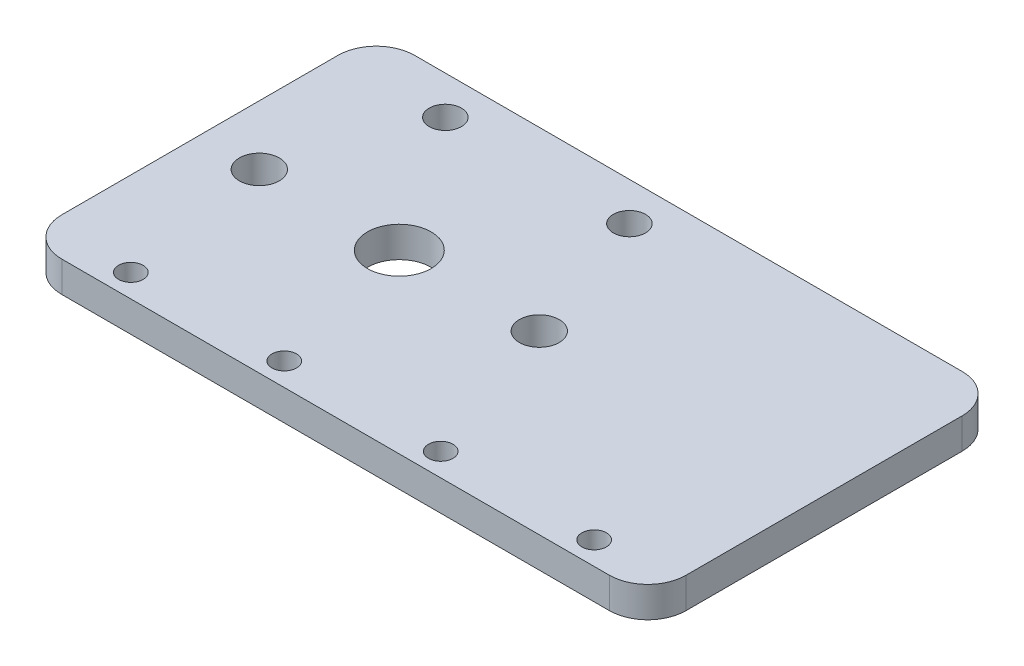
SolidWorks part; units mm, degrees
material "6061 合金"
ref_plane "前视基准面" through (0, 0, 0) normal (0, 0, 1) x (1, 0, 0)
ref_plane "上视基准面" through (0, 0, 0) normal (0, 1, 0) x (1, 0, 0)
ref_plane "右视基准面" through (0, 0, 0) normal (1, 0, 0) x (0, 0, -1)
sketch "草图1" plane through (0, 0, 0) normal (0, 1, 0) x (1, 0, 0)
  line L1 (-26, -23) -> (26, -23)
  line L2 (-26, -23) -> (-26, 23)
  line L3 (-26, 23) -> (26, 23)
  line L4 (26, -23) -> (26, 23)
  line L5 (0, 23) -> (0, -23) construction
  line L6 (-26, 0) -> (26, 0) construction
  circle A0 centre (-18.25, 0) radius 2.6
  circle A1 centre (18.25, 0) radius 2.6
  circle A2 centre (0, 0) radius 4.15
  point P0 (0, 0)
  dimension "D3" = 36.5
  dimension "D4" = 5.2
  dimension "D5" = 8.3
  dimension "D1" = 52
  dimension "D2" = 46
extrude "主板" add sketch "草图1" along normal blind 4
sketch "草图4" plane through (0, 4, 0) normal (0, 1, 0) x (1, 0, 0)
  line L0 (0, -1000) -> (0, 49000) construction
  line L1 (-1000, 0) -> (49000, 0) construction
  line L2 (-1020.8031, 18) -> (48979.1969, 18) construction
  line L4 (26, 23) -> (-26, 23) construction
  circle A0 centre (-12, 18) radius 2.1
  circle A1 centre (12, 18) radius 2.1
  circle A2 centre (12, -18) radius 2.1
  circle A3 centre (-12, -18) radius 2.1
  dimension "D2" = 4.2
  dimension "D3" = 24
  dimension "D1" = 5
extrude "垂直板接件" cut sketch "草图4" against normal through all
sketch "草图6" plane through (0, 4, 0) normal (0, 1, 0) x (1, 0, 0)
  circle A0 centre (-12, -18) radius 2.1
  circle A1 centre (12, -18) radius 2.1
  dimension "D1" = 4.2
  dimension "D2" = 4.2
extrude "凸台-拉伸1" add sketch "草图6" against normal blind 4
sketch "草图7" plane through (0, 4, 0) normal (0, 1, 0) x (1, 0, 0)
  circle A0 centre (5, -20) radius 1.2
  circle A1 centre (-15, -20) radius 1.2
  dimension "D1" = 2.4
  dimension "D2" = 2.4
extrude "切除-拉伸1" cut sketch "草图7" against normal through all
sketch "草图8" plane through (0, 0, 0) normal (0, -1, 0) x (1, 0, 0)
  line L0 (26, -23) -> (55.3847, -23)
  line L1 (26, -23) -> (26, 23)
  line L2 (26, 23) -> (55.3847, 23)
  line L3 (55.3847, 23) -> (55.3847, -23)
extrude "凸台-拉伸2" add sketch "草图8" against normal up to surface (4 mm away) up to face at (5, 4, 21.2)
fillet "圆角1" radius 5 4 edges at (-26, 2, 23) (55.3847, 2, 23) (55.3847, 2, -23) (-26, 2, -23)
sketch "草图9" plane through (0, 0, 0) normal (0, -1, 0) x (1, 0, 0)
  circle A0 centre (-15, 20) radius 1.6
  circle A1 centre (5, 20) radius 1.6
  circle A2 centre (25.4, 20) radius 1.6
  circle A3 centre (45.4, 20) radius 1.6
  point P5 (5, 20)
  point P9 (22.595, 20)
  point P12 (32.1124, 20)
  point P13 (34.5828, 10.1225)
  point P14 (39.4446, 20)
  point P15 (0, 0)
  point P16 (0, 0)
  dimension "D1" = 20.4
  dimension "D2" = 20
extrude "切除-拉伸2" cut sketch "草图9" against normal through all
